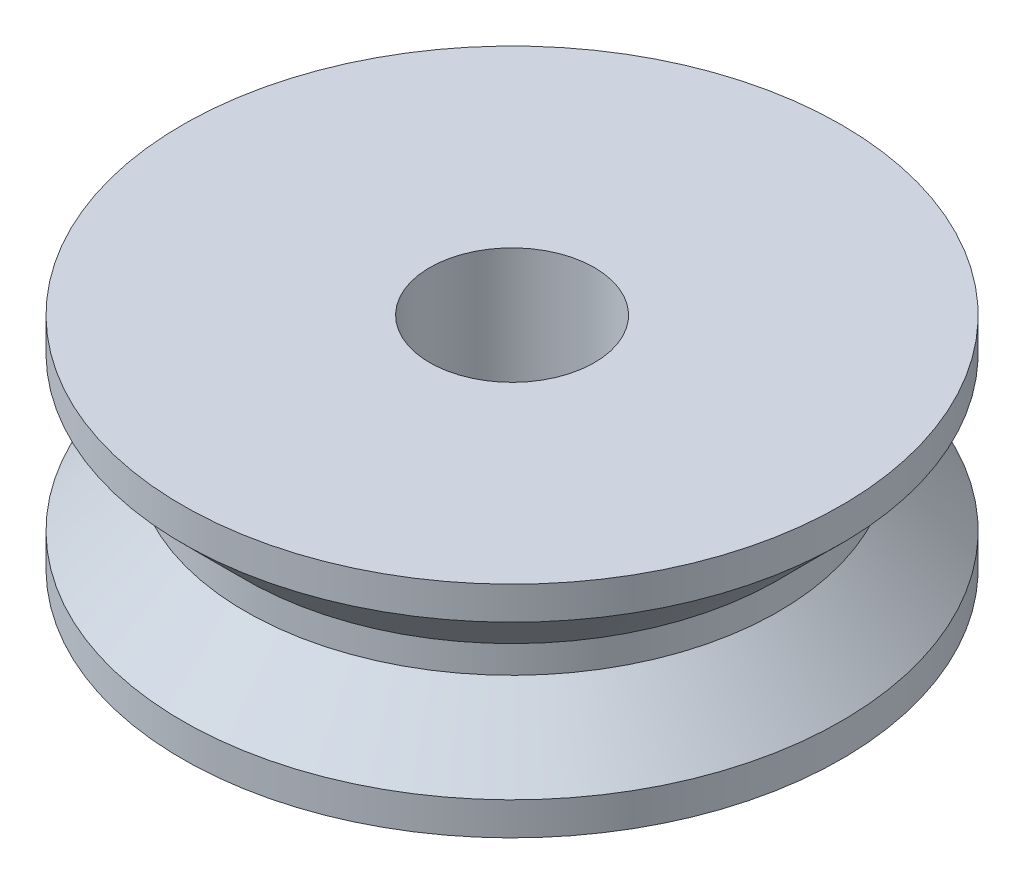
SolidWorks part; units mm, degrees
ref_plane "Plano frontal" through (0, 0, 0) normal (0, 0, 1) x (1, 0, 0)
ref_plane "Plano superior" through (0, 0, 0) normal (0, 1, 0) x (1, 0, 0)
ref_plane "Plano direito" through (0, 0, 0) normal (1, 0, 0) x (0, 0, -1)
sketch "Esboço1" plane through (0, 0, 0) normal (0, 0, 1) x (1, 0, 0)
  line L0 (1.5, 0) -> (1.5, 4)
  line L1 (1.5, 4) -> (6, 4)
  line L2 (6, 3.4) -> (4.85, 2.25)
  line L3 (4.85, 1.75) -> (6, 0.6)
  line L4 (6, 0) -> (1.5, 0)
  line L5 (0, 0) -> (0, 2.3846) construction
  line L6 (6, 4) -> (6, 3.4)
  line L7 (4.85, 2.25) -> (4.85, 1.75)
  line L8 (6, 0.6) -> (6, 0)
  dimension "D1" = 3
  dimension "D2" = 12
  dimension "D3" = 4
  dimension "D4" = 2.8
  dimension "D5" = 0.5
revolve "Revolução1" add sketch "Esboço1" angle 360 about L5
